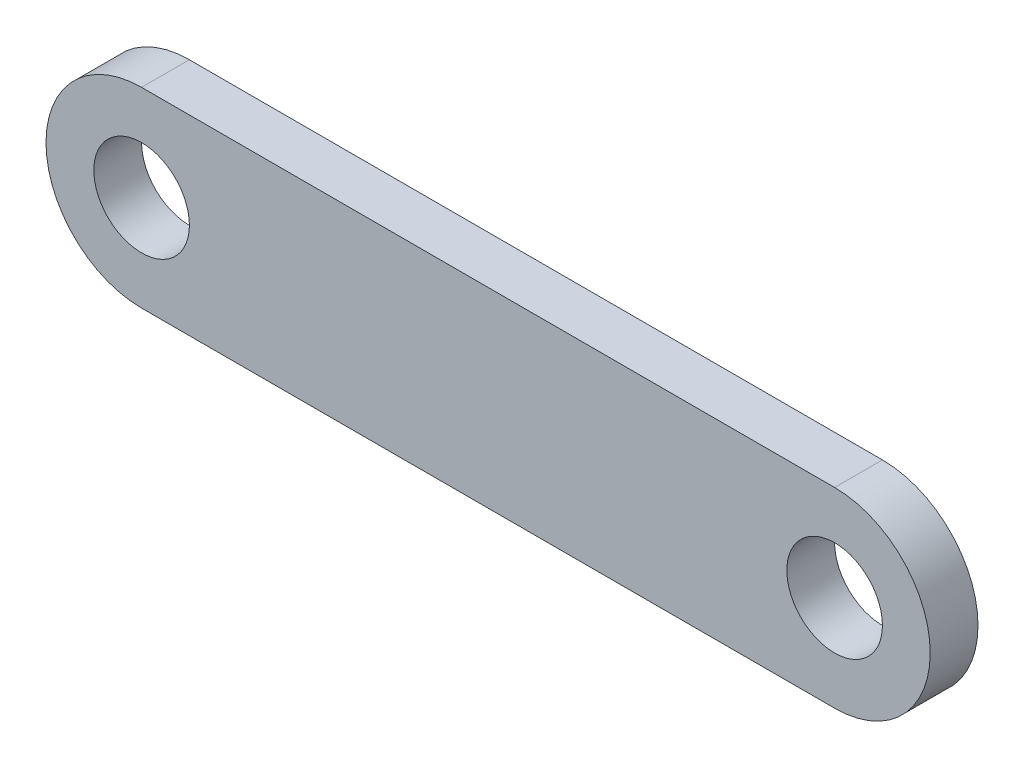
SolidWorks part; units mm, degrees
ref_plane "Front Plane" through (0, 0, 0) normal (0, 0, 1) x (1, 0, 0)
ref_plane "Top Plane" through (0, 0, 0) normal (0, 1, 0) x (1, 0, 0)
ref_plane "Right Plane" through (0, 0, 0) normal (1, 0, 0) x (0, 0, -1)
sketch "Sketch1" plane through (0, 0, 0) normal (0, 0, 1) x (1, 0, 0)
  line L0 (0, 0) -> (36.83, 0) construction
  line L1 (0, 5.08) -> (36.83, 5.08)
  line L2 (0, -5.08) -> (36.83, -5.08)
  arc A0 (0, 5.08) -> (0, -5.08) centre (0, 0) ccw
  arc A1 (36.83, -5.08) -> (36.83, 5.08) centre (36.83, 0) ccw
  circle A2 centre (0, 0) radius 2.54
  circle A3 centre (36.83, 0) radius 2.54
  point P3 (18.415, 0)
  dimension "D2" = 5.08
  dimension "D3" = 5.08
  dimension "D4" = 5.08
  dimension "D1" = 36.83
extrude "Boss-Extrude1" add sketch "Sketch1" along normal blind 2.54
